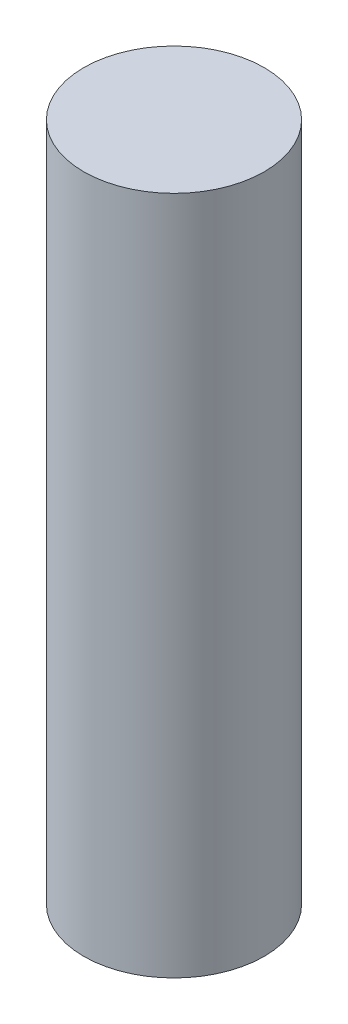
SolidWorks part; units mm, degrees
ref_plane "Front Plane" through (0, 0, 0) normal (0, 0, 1) x (1, 0, 0)
ref_plane "Top Plane" through (0, 0, 0) normal (0, 1, 0) x (1, 0, 0)
ref_plane "Right Plane" through (0, 0, 0) normal (1, 0, 0) x (0, 0, -1)
sketch "Sketch1" plane through (0, 0, 0) normal (0, 1, 0) x (1, 0, 0)
  circle A0 centre (0, 0) radius 4.25
  dimension "D1" = 8.5
extrude "Boss-Extrude1" add sketch "Sketch1" along normal blind 32
